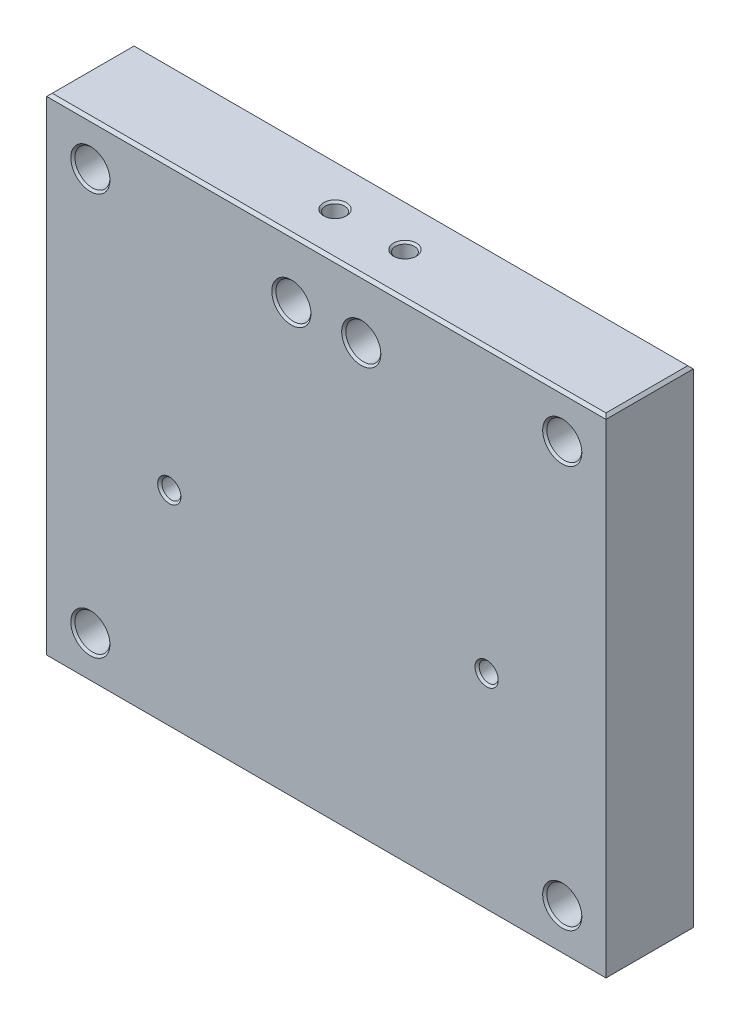
SolidWorks part; units mm, degrees
material "Brass"
ref_plane "Front Plane" through (0, 0, 0) normal (0, 0, 1) x (1, 0, 0)
ref_plane "Top Plane" through (0, 0, 0) normal (0, 1, 0) x (1, 0, 0)
ref_plane "Right Plane" through (0, 0, 0) normal (1, 0, 0) x (0, 0, -1)
sketch "Sketch1" plane through (0, 0, 0) normal (0, 0, 1) x (1, 0, 0)
  line L1 (0, 0) -> (-101.6, 0)
  line L2 (0, 0) -> (0, 88.9)
  line L3 (0, 88.9) -> (-101.6, 88.9)
  line L4 (-101.6, 0) -> (-101.6, 88.9)
  dimension "D1" = 101.6
  dimension "D2" = 88.9
extrude "Boss-Extrude1" add sketch "Sketch1" along normal blind 15.875
sketch "Sketch5" plane through (0, 88.9, 0) normal (0, 1, 0) x (1, 0, 0)
  line L0 (-101.6, -7.9375) -> (0, -7.9375) construction
  line L1 (-101.6, -15.875) -> (-101.6, 0) construction
  line L2 (0, -15.875) -> (0, 0) construction
  line L3 (-57.15, -7.9375) -> (-44.45, -7.9375)
  point P8 (-50.8, -7.9375)
  dimension "D1" = 12.7
hole_wizard "#8-32 Tapped Hole1" positions "Sketch6" profile "Sketch8" tap size "#8-32" standard "ANSI Inch"
sketch "Sketch6" plane through (0, 88.9, 0) normal (0, 1, 0) x (1, 0, 0)
  point P0 (-44.45, -7.9375)
  point P3 (-57.15, -7.9375)
sketch "Sketch8" plane through (-44.45, 88.9, 7.9375) normal (1, 0, 0) x (0, 0, 1)
  line L0 (0, 0) -> (0, 10.6898)
  line L1 (0, 10.6898) -> (1.7272, 9.652)
  line L2 (1.7272, 9.652) -> (1.7272, 0.3556)
  line L3 (1.7272, 0.3556) -> (2.0828, 0)
  line L5 (2.0828, 0) -> (0, 0)
  line L6 (-1.7272, 0.3556) -> (-2.0828, 0) construction
  line L10 (0, 10.6898) -> (-1.7272, 9.652) construction
  line L11 (0, -6.35) -> (0, 107.95) construction
  dimension "Tap Drill Dia." = 3.4544
  dimension "Tap Drill Depth" = 9.652
  dimension "Near C'Sink Dia." = 4.1656
  dimension "Near C'Sink Angle" = 90
  dimension "Drill Angle" = 118
cosmetic thread "Hole Thread1" parameters "D1"=9.2511, "D2"=4.1656
cosmetic thread "Hole Thread2" parameters "D1"=9.2511, "D2"=4.1656
hole_wizard "1/4 (0.25) Diameter Hole1" positions "Sketch11" profile "Sketch12" hole size "1/4" standard "ANSI Inch"
sketch "Sketch11" plane through (0, 0, 15.875) normal (0, 0, 1) x (1, 0, 0)
  line L0 (-44.45, 78.2102) -> (-42.7228, 79.248) construction
  line L1 (-57.15, 78.2102) -> (-55.4228, 79.248) construction
  line L2 (-44.45, 78.2102) -> (-42.7228, 79.248)
  line L3 (-57.15, 78.2102) -> (-55.4228, 79.248)
  point P1 (-44.45, 78.2102)
  point P3 (-57.15, 78.2102)
sketch "Sketch12" plane through (-44.45, 78.2102, 15.875) normal (1, 0, 0) x (0, -1, 0)
  line L0 (0, 0) -> (0, 27.3077)
  line L1 (0, 27.3077) -> (3.175, 25.4)
  line L2 (3.175, 25.4) -> (3.175, 0)
  line L5 (3.175, 0) -> (0, 0)
  line L10 (0, 27.3077) -> (-3.175, 25.4) construction
  line L11 (0, -6.35) -> (0, 107.95) construction
  dimension "Hole Dia." = 6.35
  dimension "Hole Depth" = 25.4
  dimension "Drill Angle" = 118
sketch "Sketch13" plane through (0, 0, 15.875) normal (0, 0, 1) x (1, 0, 0)
  line L8 (-6.35, 6.35) -> (-6.35, 82.55)
  line L9 (-6.35, 82.55) -> (-95.25, 82.55)
  line L10 (-95.25, 82.55) -> (-95.25, 6.35)
  line L11 (-95.25, 6.35) -> (-6.35, 6.35)
  line L12 (-6.35, 6.35) -> (-6.35, 82.55)
  line L13 (-6.35, 82.55) -> (-95.25, 82.55)
  line L14 (-95.25, 82.55) -> (-95.25, 6.35)
  line L15 (-95.25, 6.35) -> (-6.35, 6.35)
  dimension "D1" = 6.35
sketch "Sketch17" plane through (0, 0, 15.875) normal (0, 0, 1) x (1, 0, 0)
  line L0 (-82.55, 12.7) -> (-19.05, 12.7)
  line L1 (-82.55, 12.7) -> (-101.6, 12.7)
  line L2 (-101.6, 88.9) -> (-101.6, 0) construction
  line L3 (-19.05, 12.7) -> (0, 12.7)
  line L4 (0, 0) -> (0, 88.9) construction
  line L5 (-101.6, 0) -> (0, 0) construction
  dimension "D1" = 63.5
  dimension "D2" = 12.7
hole_wizard "#8-32 Tapped Hole2" positions "Sketch21" profile "Sketch22" tap size "#8-32" standard "ANSI Inch" end condition through all
sketch "Sketch21" plane through (0, 0, 0) normal (0, 0, -1) x (-1, 0, 0)
  line L9 (5.8, 8.89) -> (95.8, 8.89)
  line L10 (5.8, 66.294) -> (5.8, 8.89)
  line L11 (95.8, 66.294) -> (5.8, 66.294)
  line L12 (95.8, 8.89) -> (95.8, 66.294)
  line L13 (5.8, 8.89) -> (95.8, 8.89)
  line L14 (5.8, 66.294) -> (5.8, 8.89)
  line L15 (95.8, 66.294) -> (5.8, 66.294)
  line L16 (95.8, 8.89) -> (95.8, 66.294)
  circle A4 centre (21.675, 37.592) radius 2.2479
  circle A5 centre (21.675, 37.592) radius 2.2479
  circle A8 centre (79.3203, 37.592) radius 2.2479
  circle A9 centre (79.3203, 37.592) radius 2.2479
  point P53 (79.3203, 37.592)
  point P56 (21.675, 37.592)
  dimension "D1" = 0
  dimension "D2" = 0
  dimension "D3" = 0
sketch "Sketch22" plane through (-21.675, 37.592, 0) normal (1, 0, 0) x (0, 1, 0)
  line L0 (0, 0) -> (0, 15.875)
  line L1 (0, 15.875) -> (1.7272, 15.875)
  line L2 (1.7272, 15.875) -> (1.7272, 0)
  line L5 (1.7272, 0) -> (0, 0)
  line L11 (0, -6.35) -> (0, 107.95) construction
  dimension "Thru Tap Drill Dia." = 3.4544
  dimension "Thru Tap Drill Depth" = 15.875
cosmetic thread "Hole Thread7" parameters "D2"=4.1656
cosmetic thread "Hole Thread8" parameters "D2"=4.1656
hole_wizard "#9 (0.196) Diameter Hole1" positions "Sketch25" profile "Sketch26" hole size "#9" standard "ANSI Inch"
sketch "Sketch25" plane through (0, 0, 0) normal (0, -1, 0) x (-1, 0, 0)
  line L0 (76.2, -7.9375) -> (25.4, -7.9375)
  line L2 (0, -15.875) -> (0, 0) construction
  line L3 (101.6, -15.875) -> (101.6, 0) construction
  line L4 (76.2, -7.9375) -> (101.6, -7.9375) construction
  line L6 (25.4, -7.9375) -> (0, -7.9375) construction
  point P1 (76.2, -7.9375)
  point P2 (25.4, -7.9375)
  point P6 (0, -7.9375)
  dimension "D1" = 50.8
sketch "Sketch26" plane through (-76.2, 0, 7.9375) normal (1, 0, 0) x (0, 0, -1)
  line L0 (0, 0) -> (0, 14.1957)
  line L1 (0, 14.1957) -> (2.4892, 12.7)
  line L2 (2.4892, 12.7) -> (2.4892, 0)
  line L5 (2.4892, 0) -> (0, 0)
  line L10 (0, 14.1957) -> (-2.4892, 12.7) construction
  line L11 (0, -6.35) -> (0, 107.95) construction
  dimension "Hole Dia." = 4.9784
  dimension "Hole Depth" = 12.7
  dimension "Drill Angle" = 118
hole_wizard "Hole1" positions "Sketch27" profile "Sketch29" legacy end condition through all
sketch "Sketch27" plane through (0, 0, 0) normal (0, 0, 1) x (1, 0, 0)
  line L1 (-93.6625, 80.9625) -> (-7.9375, 80.9625)
  line L2 (-93.6625, 80.9625) -> (-93.6625, 7.9375)
  line L3 (-93.6625, 7.9375) -> (-7.9375, 7.9375)
  line L4 (-7.9375, 80.9625) -> (-7.9375, 7.9375)
  line L5 (-93.6625, 80.9625) -> (-7.9375, 7.9375) construction
  line L6 (-93.6625, 7.9375) -> (-7.9375, 80.9625) construction
  line L7 (-101.6, 88.9) -> (0, 0) construction
  line L9 (-93.6625, 44.45) -> (-101.6, 44.45) construction
  line L10 (-101.6, 88.9) -> (-101.6, 0) construction
  line L12 (-50.8, 7.9375) -> (-50.8, 0) construction
  line L14 (-101.6, 0) -> (0, 0) construction
  point P2 (-7.9375, 7.9375)
  point P5 (-93.6625, 80.9625)
  point P6 (-93.6625, 7.9375)
  point P7 (-7.9375, 80.9625)
  dimension "D1" = 7.9375
sketch "Sketch29" plane through (-7.9375, 7.9375, 0) normal (1, 0, 0) x (0, 1, 0)
  line L0 (0, 0) -> (0, 17.7827)
  line L1 (0, 17.7827) -> (3.175, 15.875)
  line L2 (3.175, 15.875) -> (3.175, 9.525)
  line L3 (3.175, 9.525) -> (4.7625, 9.525)
  line L4 (4.7625, 0) -> (0, 0)
  line L5 (0, -11.3109) -> (0, 121.1557) construction
  line L6 (0, 17.7827) -> (-3.175, 15.875) construction
  line L7 (4.7625, 9.525) -> (4.7625, 0)
  dimension "Depth" = 15.875
  dimension "Drill Angle" = 118
  dimension "Diameter" = 6.35
  dimension "C-Bore Diameter" = 9.525
  dimension "C-Bore Depth" = 9.525
chamfer "Chamfer1" distance 0.508 angle 45 12 edges at (-101.6, 0, 7.9375) (-50.8, 0, 15.875) (-50.8, 0, 0) (0, 0, 7.9375) (0, 44.45, 15.875) (0, 44.45, 0) (0, 88.9, 7.9375) (-101.6, 44.45, 0) (-50.8, 88.9, 0) (-50.8, 88.9, 15.875) (-101.6, 88.9, 7.9375) (-101.6, 44.45, 15.875)
chamfer "Chamfer2" distance 0.381 angle 45 16 edges at (-11.1125, 7.9375, 15.875) (-96.8375, 7.9375, 15.875) (-81.0475, 37.592, 15.875) (-23.4022, 37.592, 15.875) (-96.8375, 80.9625, 15.875) (-53.975, 78.2102, 15.875) (-41.275, 78.2102, 15.875) (-11.1125, 80.9625, 15.875) (-12.7, 80.9625, 0) (-12.7, 7.9375, 0) (-23.4022, 37.592, 0) (-81.0475, 37.592, 0) (-41.275, 78.2102, 0) (-53.975, 78.2102, 0) (-98.425, 80.9625, 0) (-98.425, 7.9375, 0)
